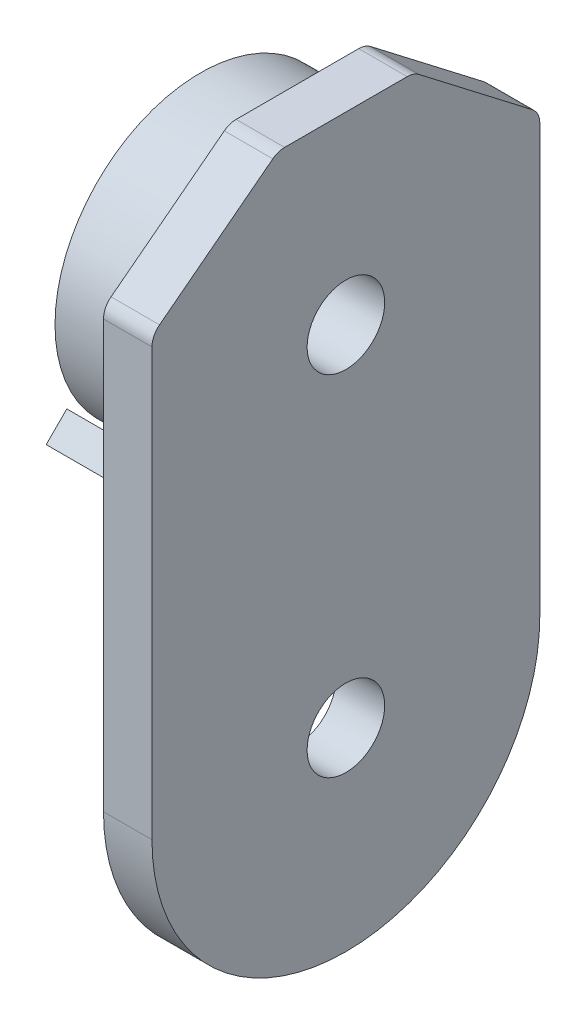
SolidWorks part; units mm, degrees
ref_plane "Ebene vorne" through (0, 0, 0) normal (0, 0, 1) x (1, 0, 0)
ref_plane "Ebene oben" through (0, 0, 0) normal (0, 1, 0) x (1, 0, 0)
ref_plane "Ebene rechts" through (0, 0, 0) normal (1, 0, 0) x (0, 0, -1)
sketch "Skizze1" plane through (0, 0, 0) normal (1, 0, 0) x (0, 0, -1)
  line L0 (0, 0) -> (0, 55) construction
  line L2 (-20, 0) -> (-20, 45)
  line L3 (-7, 55) -> (7, 55)
  line L4 (20, 0) -> (20, 45)
  line L5 (-20, 45) -> (-7, 55)
  line L6 (7, 55) -> (20, 45)
  arc A0 (-20, 0) -> (20, 0) centre (0, 0) ccw
  point P4 (0, 55)
  dimension "D1" = 40
  dimension "D2" = 75
  dimension "D3" = 10
  dimension "D4" = 13
extrude "Aufsatz-Linear austragen1" add sketch "Skizze1" against normal blind 5
fillet "Verrundung2" radius 2 4 edges at (-2.5, 45, -20) (-2.5, 55, -7) (-2.5, 55, 7) (-2.5, 45, 20)
sketch "Skizze7" plane through (-5, 0, 0) normal (-1, 0, 0) x (0, 0, 1)
  line L0 (-6.3198, 55) -> (6.3198, 55) construction
  line L4 (0, 36) -> (0, 54) construction
  circle A0 centre (0, 36) radius 15
  dimension "D1" = 30
  dimension "D2" = 19
  dimension "D4" = 18
extrude "Aufsatz-Linear austragen3" add sketch "Skizze7" along normal blind 10 contours A0
sketch "Skizze8" plane through (-5, 0, 0) normal (-1, 0, 0) x (0, 0, 1)
  line L0 (0, 0) -> (0, 36) construction
  line L1 (0, 36) -> (13.0815, 22.9185) construction
  line L2 (15.9099, 25.747) -> (10.253, 20.0901)
  line L3 (15.9099, 25.747) -> (13.7829, 27.874)
  line L4 (10.253, 20.0901) -> (8.126, 22.2171)
  arc A1 (8.126, 22.2171) -> (13.7829, 27.874) centre (0, 36) ccw
  circle A3 centre (0, 36) radius 15 construction
  point P8 (13.0815, 22.9185)
  dimension "D1" = 1
  dimension "D3" = 45
  dimension "D4" = 18.5
  dimension "D5" = 8
extrude "Aufsatz-Linear austragen5" add sketch "Skizze8" along normal blind 10
mirror "Spiegeln2" about plane through (0, 0, 0) normal (0, 0, 1) of "Aufsatz-Linear austragen5"
sketch "Skizze9" plane through (-15, 0, 0) normal (-1, 0, 0) x (0, 0, 1)
  circle A0 centre (0, 36) radius 4
  dimension "D1" = 8
extrude "Schnitt-Linear austragen2" cut sketch "Skizze9" against normal up to next
sketch "Skizze10" plane through (-5, 0, 0) normal (-1, 0, 0) x (0, 0, 1)
  circle A0 centre (0, 0) radius 4
  dimension "D1" = 8
extrude "Schnitt-Linear austragen3" cut sketch "Skizze10" against normal up to next
